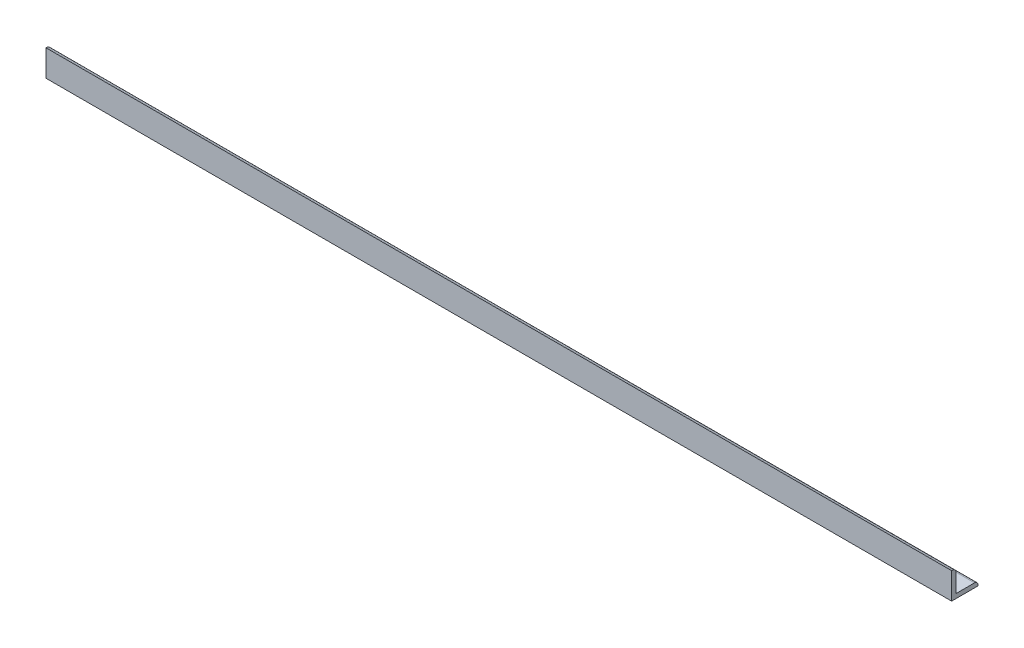
SolidWorks part; units mm, degrees
ref_plane "Front" through (0, 0, 0) normal (0, 0, 1) x (1, 0, 0)
ref_plane "Top" through (0, 0, 0) normal (0, 1, 0) x (1, 0, 0)
ref_plane "Right" through (0, 0, 0) normal (1, 0, 0) x (0, 0, -1)
sketch "Sketch1" plane through (0, 0, 0) normal (1, 0, 0) x (0, 0, -1)
  line L0 (3.175, 3.175) -> (16.51, 3.175)
  line L1 (0, 0) -> (19.05, 0)
  line L2 (0, 0) -> (0, 19.05)
  line L5 (3.175, 3.175) -> (3.175, 16.51)
  line L6 (19.05, 0) -> (19.05, 0.635)
  line L7 (0, 19.05) -> (0.635, 19.05)
  line L8 (3.175, 3.175) -> (3.175, 19.05) construction
  line L9 (3.175, 3.175) -> (19.05, 3.175) construction
  arc A0 (3.175, 16.51) -> (0.635, 19.05) centre (0.635, 16.51) ccw
  arc A1 (16.51, 3.175) -> (19.05, 0.635) centre (16.51, 0.635) cw
  point P5 (0, 0)
  dimension "D3" = 2.54
  dimension "D1" = 19.05
  dimension "D2" = 3.175
extrude "Boss-Extrude1" add sketch "Sketch1" along normal blind 654.0729
sketch "Sketch2" plane through (0, 3.175, 0) normal (0, 1, 0) x (1, 0, 0)
  line L0 (654.0729, 9.8425) -> (641.3729, 9.8425) construction
  line L1 (654.0729, 16.51) -> (654.0729, 3.175) construction
  line L2 (641.3729, 9.8425) -> (12.7, 9.8425) construction
  circle A0 centre (641.3729, 9.8425) radius 2.54
  circle A1 centre (12.7, 9.8425) radius 2.54
  dimension "D2" = 5.08
  dimension "D4" = 5.08
  dimension "D1" = 12.7
  dimension "D3" = 628.6729
extrude "Cut-Extrude1" cut sketch "Sketch2" against normal up to next
